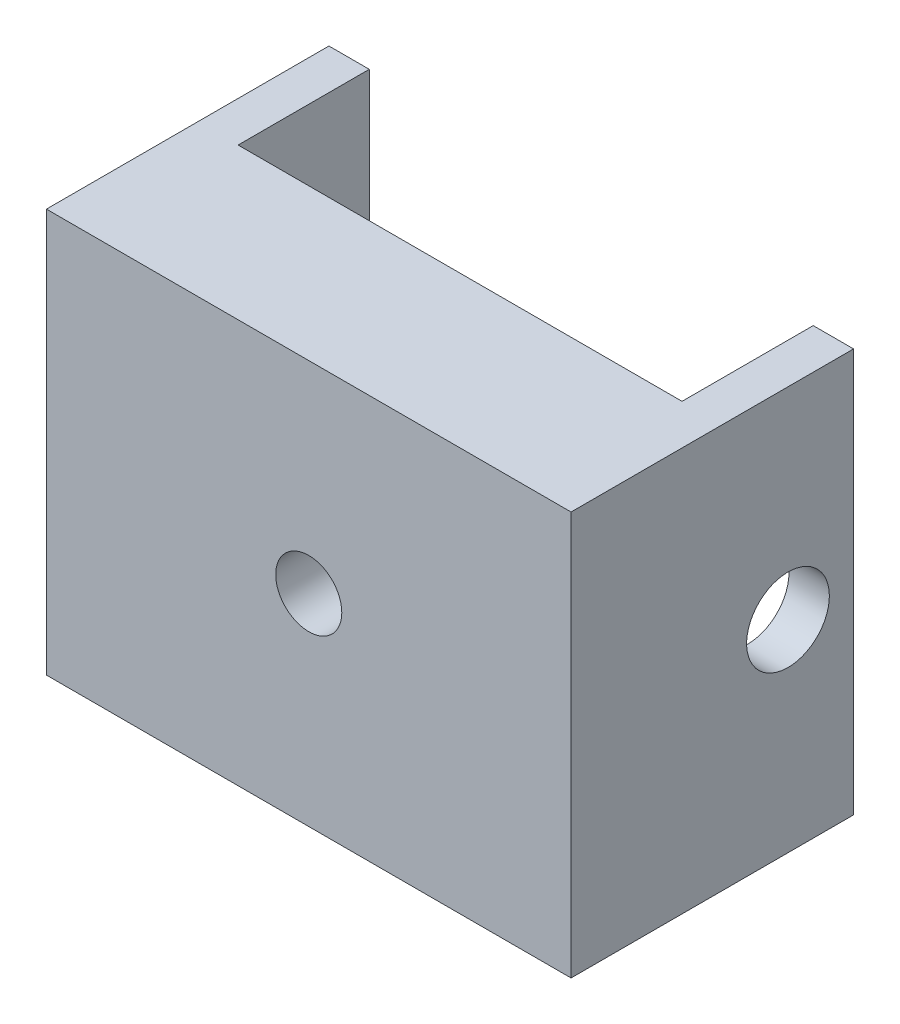
SolidWorks part; units mm, degrees
ref_plane "Front Plane" through (0, 0, 0) normal (0, 0, 1) x (1, 0, 0)
ref_plane "Top Plane" through (0, 0, 0) normal (0, 1, 0) x (1, 0, 0)
ref_plane "Right Plane" through (0, 0, 0) normal (1, 0, 0) x (0, 0, -1)
sketch "Sketch1" plane through (0, 0, 0) normal (0, 1, 0) x (1, 0, 0)
  line L0 (0, 0) -> (0, 12.0463) construction
  line L1 (0, 0) -> (-17.0451, 0) construction
  line L2 (-13, 6.0686) -> (-13, -6.5455) construction
  line L3 (11, -5) -> (-11, -5)
  line L4 (11, -5) -> (11, 5)
  line L5 (11, 5) -> (-11, 5)
  line L6 (-11, -5) -> (-11, 5)
  line L7 (11, -5) -> (-11, 5) construction
  line L8 (11, 5) -> (-11, -5) construction
  line L9 (13, 5.5676) -> (13, -6.5455) construction
  line L10 (-12.6924, 9) -> (9.3824, 9) construction
  line L11 (-11, -5) -> (-13, -5)
  line L12 (-13, -5) -> (-13, 9)
  line L13 (-13, 9) -> (-11, 9)
  line L14 (-11, 9) -> (-11, -5)
  line L15 (11, 9) -> (11, -5)
  line L16 (13, 9) -> (11, 9)
  line L17 (13, -5) -> (13, 9)
  line L18 (11, -5) -> (13, -5)
  line L19 (11, -5) -> (11, 5)
  line L20 (-13.7445, 2.5) -> (12.5747, 2.5) construction
  line L21 (-11, 2.5) -> (11, 2.5)
  point P1 (0, 0)
  dimension "D1" = 10
  dimension "D2" = 22
  dimension "D3" = 2
  dimension "D4" = 2
  dimension "D5" = 4
  dimension "D6" = 2.5
extrude "Boss-Extrude1" add sketch "Sketch1" along normal blind 20 contours L6 L3 L4 L5 | L14 L13 L12 L11 L6 | L4 L18 L17 L16 L15
sketch "Sketch3" plane through (0, 0, 0) normal (0, 0, 1) x (1, 0, 0)
  line L0 (0, 0) -> (0, 18.3275) construction
  line L1 (0, 0) -> (-13.1169, 0) construction
  line L2 (-3.2033, 20) -> (-13.6827, 20) construction
  line L4 (-13.1169, 10) -> (13.2537, 10) construction
  circle A0 centre (0, 10) radius 1.6375
  dimension "D3" = 3.275
  dimension "D1" = 20
  dimension "D2" = 10
extrude "Cut-Extrude1" cut sketch "Sketch3" against normal through all and the other way through all
sketch "Sketch7" plane through (0, 0, 0) normal (1, 0, 0) x (0, 0, -1)
  line L0 (0, 0) -> (0, 18.5502) construction
  line L1 (0, 0) -> (14.4213, 0) construction
  line L2 (2.5, 17.989) -> (2.5, -0.6901) construction
  line L3 (9, 5.2035) -> (9, -6.1649) construction
  line L4 (-6.0726, 10) -> (18.1473, 10) construction
  line L5 (-5, 3.3358) -> (-5, -7.0988) construction
  line L6 (5.75, 18.6041) -> (5.75, -0.9952) construction
  line L7 (3.0909, 20) -> (15.1586, 20) construction
  circle A0 centre (5.75, 10) radius 2.05
  dimension "D7" = 4.1
  dimension "D1" = 14
  dimension "D2" = 6.5
  dimension "D3" = 9
  dimension "D4" = 20
  dimension "D5" = 10
  dimension "D6" = 3.25
extrude "Cut-Extrude2" cut sketch "Sketch7" against normal through all and the other way through all
